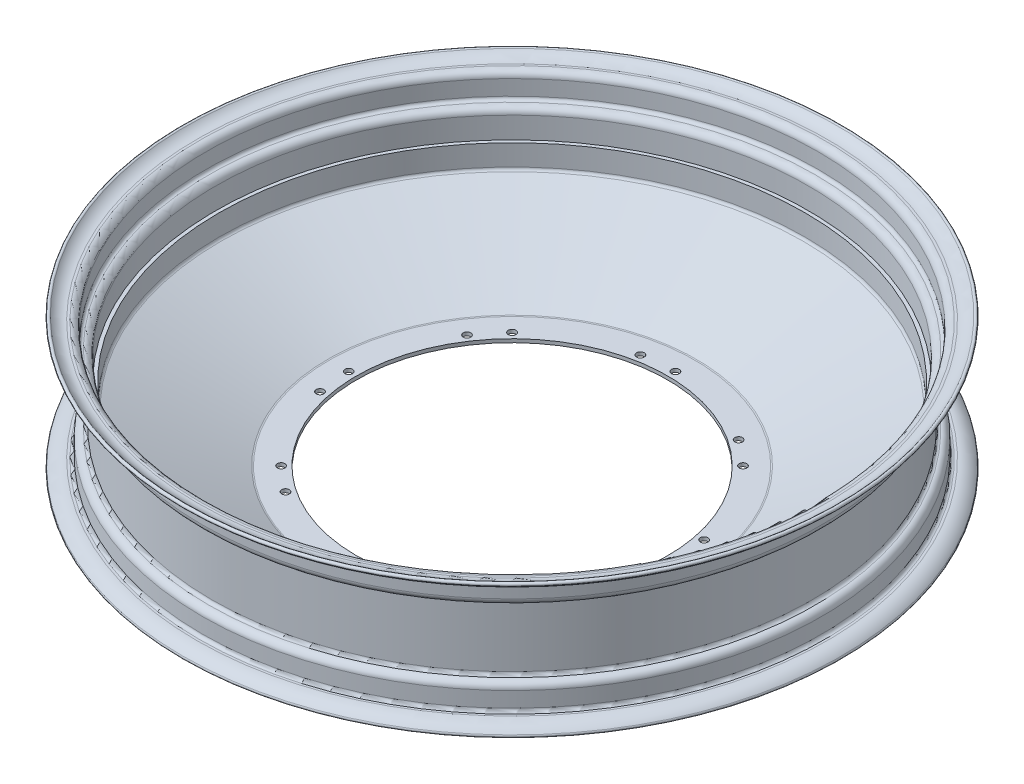
SolidWorks part; units mm, degrees
material "6061-T6 (SS)"
ref_plane "Front Plane" through (0, 0, 0) normal (0, 0, 1) x (1, 0, 0)
ref_plane "Top Plane" through (0, 0, 0) normal (0, 1, 0) x (1, 0, 0)
ref_plane "Right Plane" through (0, 0, 0) normal (1, 0, 0) x (0, 0, -1)
sketch "Sketch3" plane through (0, 0, 0) normal (0, 0, 1) x (1, 0, 0)
  line L0 (-167.2903, -3.117) -> (0, 0) construction
  line L2 (-206.3572, 37.168) -> (-204.8586, 37.168)
  line L3 (-200.5767, 32.8816) -> (-200.587, 22.8667)
  line L9 (-198.587, 19.7217) -> (-186.9755, 19.7217) construction
  line L13 (-102, -47.2925) -> (-119.8323, -47.2925)
  line L15 (-121.5965, -46.912) -> (-191.4766, -15.2967)
  line L17 (-194.301, 2.5281) -> (-192.015, 2.5281)
  line L18 (-200.4193, -21.368) -> (-183.6675, -4.616) construction
  line L24 (-202.8627, 32.884) -> (-202.873, 22.8691)
  line L26 (-206.3572, 34.882) -> (-204.8586, 34.882)
  line L35 (-102, -45.0056) -> (-102, -47.2925)
  line L36 (-200.4029, 15.0741) -> (-183.65, -1.6215) construction
  line L37 (-167.2903, -3.117) -> (-212.0495, -3.117) construction
  line L40 (-200.5767, 32.8816) -> (-200.589, 20.8706) construction
  line L41 (0, 240.889) -> (0, -99.5724) construction
  line L44 (-178.7195, -0.4999) -> (-178.7213, -5.7331) construction
  line L45 (-192.015, 2.5281) -> (-192.015, -11.2538)
  line L46 (-119.8323, -45.0065) -> (-102, -45.0056)
  line L47 (-181.0064, -3.0207) -> (-181.0064, -3.2073) construction
  line L48 (-198.8067, 16.7107) -> (-182.0364, -0.0021) construction
  line L49 (-198.8174, -22.999) -> (-182.0511, -6.2324) construction
  line L53 (-194.301, 16.5787) -> (-194.301, 2.5281)
  line L54 (-196.587, 16.5766) -> (-196.587, -22.8107)
  line L55 (-202.8627, 32.884) -> (-202.875, 20.8729) construction
  line L56 (-198.587, 20.8647) -> (-198.587, 18.5787) construction
  line L57 (-198.587, -27.0988) -> (-198.587, -24.8128) construction
  line L62 (-200.5711, -39.118) -> (-200.5712, -27.1182) construction
  line L63 (-206.3572, -43.404) -> (-204.8571, -43.404) construction
  line L64 (-202.8571, -39.118) -> (-202.8572, -27.1182) construction
  line L65 (-206.3572, -41.118) -> (-204.8571, -41.118) construction
  line L66 (-198.587, -25.9558) -> (-186.9755, -25.9558) construction
  line L67 (-206.3572, -41.1161) -> (-204.8586, -41.1161)
  line L68 (-202.8627, -39.1181) -> (-202.873, -29.1032)
  line L69 (-200.5767, -39.1157) -> (-200.587, -29.1008)
  line L70 (-206.3572, -43.4021) -> (-204.8586, -43.4021)
  line L72 (-120.6542, -44.8292) -> (-190.8394, -13.0759)
  line L73 (-120.6542, -44.8292) -> (-193.3587, -11.9362) construction
  line L74 (-104.286, -45.0065) -> (-119.8323, -45.0065) construction
  line L75 (-194.301, -17.1189) -> (-194.301, -22.8128)
  line L76 (-121.5965, -46.912) -> (-194.301, -14.0189) construction
  line L77 (-104.286, -45.0056) -> (-104.286, -45.0065) construction
  arc A0 (-213.9267, 40.5243) -> (-206.3572, 37.168) centre (-206.3572, 47.382) ccw
  arc A1 (-200.5767, 32.8816) -> (-204.8586, 37.168) centre (-204.8586, 32.886) ccw
  arc A11 (-182.0364, -0.0021) -> (-178.7195, -0.4999) centre (-180.0399, 2.0022) ccw construction
  arc A12 (-119.8323, -47.2925) -> (-121.5965, -46.912) centre (-119.8323, -43.0125) cw
  arc A13 (-178.7213, -5.7331) -> (-182.0511, -6.2324) centre (-180.0485, -8.2349) ccw construction
  arc A14 (-213.9267, 40.5243) -> (-215.6209, 38.9895) centre (-214.7738, 39.7569) ccw
  arc A17 (-183.65, -1.6215) -> (-181.0064, -3.0207) centre (-180.0399, 2.0022) ccw construction
  arc A24 (-202.8627, 32.884) -> (-204.8586, 34.882) centre (-204.8586, 32.886) ccw
  arc A28 (-215.6209, 38.9895) -> (-206.3572, 34.882) centre (-206.3572, 47.382) ccw
  arc A31 (-181.0064, -3.2073) -> (-183.6675, -4.616) centre (-180.0485, -8.2349) ccw construction
  arc A37 (-200.589, 20.8706) -> (-198.8067, 16.7107) centre (-194.8572, 20.8647) ccw construction
  arc A38 (-202.875, 20.8729) -> (-200.4029, 15.0741) centre (-194.8572, 20.8647) ccw construction
  arc A42 (-198.587, 20.8647) -> (-200.587, 22.8667) centre (-198.587, 22.8647) cw
  arc A44 (-202.873, 22.8691) -> (-198.587, 18.5787) centre (-198.587, 22.8647) ccw
  arc A49 (-119.8323, -45.0065) -> (-120.6542, -44.8292) centre (-119.8323, -43.0125) cw
  arc A54 (-198.587, -27.0988) -> (-194.301, -22.8128) centre (-198.587, -22.8128) ccw
  arc A55 (-198.587, -24.8128) -> (-196.587, -22.8107) centre (-198.587, -22.8128) ccw
  arc A56 (-198.587, 18.5787) -> (-196.587, 16.5766) centre (-198.587, 16.5787) cw
  arc A57 (-198.587, 20.8647) -> (-194.301, 16.5787) centre (-198.587, 16.5787) cw
  arc A58 (-198.8174, -22.999) -> (-200.5712, -27.1182) centre (-194.8572, -27.1181) ccw construction
  arc A59 (-204.8571, -43.404) -> (-200.5711, -39.118) centre (-204.8571, -39.118) ccw construction
  arc A60 (-206.3572, -43.404) -> (-213.9267, -46.7603) centre (-206.3572, -53.618) ccw construction
  arc A61 (-204.8571, -41.118) -> (-202.8571, -39.118) centre (-204.8571, -39.118) ccw construction
  arc A62 (-200.4193, -21.368) -> (-202.8572, -27.1182) centre (-194.8572, -27.1181) ccw construction
  arc A63 (-206.3572, -41.118) -> (-215.6209, -45.2255) centre (-206.3572, -53.618) ccw construction
  arc A64 (-198.587, -24.8128) -> (-202.873, -29.1032) centre (-198.587, -29.0988) ccw
  arc A65 (-198.587, -27.0988) -> (-200.587, -29.1008) centre (-198.587, -29.0988) ccw
  arc A66 (-215.6209, -45.2236) -> (-206.3572, -41.1161) centre (-206.3572, -53.6161) cw
  arc A67 (-202.8627, -39.1181) -> (-204.8586, -41.1161) centre (-204.8586, -39.1201) cw
  arc A68 (-213.9267, -46.7584) -> (-215.6209, -45.2236) centre (-214.7738, -45.991) cw
  arc A69 (-200.5767, -39.1157) -> (-204.8586, -43.4021) centre (-204.8586, -39.1201) cw
  arc A70 (-213.9267, -46.7584) -> (-206.3572, -43.4021) centre (-206.3572, -53.6161) cw
  arc A71 (-192.015, -11.2538) -> (-190.8394, -13.0759) centre (-190.015, -11.2538) ccw
  arc A72 (-191.4766, -15.2967) -> (-194.301, -17.1189) centre (-192.301, -17.1189) ccw
  point P103 (-194.301, -3.117)
  point P121 (-196.587, -3.117)
  point P130 (-194.301, -14.0189)
  dimension "D1" = 41.8885
  dimension "D3" = 4.282
  dimension "D8" = 4.28
  dimension "D5" = 1.996
  dimension "D6" = 2
  dimension "D9" = 2
  dimension "D10" = 2
  dimension "D2" = 2.286
  dimension "D4" = 2.286
revolve "Revolve2" add sketch "Sketch3" angle 360 about L41
sketch "Sketch4" plane through (0, 0, 0) normal (0, 1, 0) x (1, 0, 0)
  line L0 (0, 0) -> (0, 107) construction
  line L1 (0, 0) -> (-20.8747, 104.944) construction
  circle A0 centre (0, 107) radius 2.5
  circle A1 centre (-3884.1816, -9484.2438) radius 2.5
  circle A2 centre (-13412.7463, -13519.7463) radius 2.5
  circle A3 centre (-23003.9901, -9635.5647) radius 2.5
  circle A4 centre (-27039.4925, -107) radius 2.5
  circle A5 centre (-23155.3109, 9484.2438) radius 2.5
  circle A6 centre (-13626.7463, 13519.7463) radius 2.5
  circle A7 centre (-4035.5024, 9635.5647) radius 2.5
  circle A8 centre (-20.8747, 104.944) radius 2.5
  circle A9 centre (-3900.396, -9470.937) radius 2.5
  circle A10 centre (-13414.8022, -13498.8716) radius 2.5
  circle A11 centre (-22990.6833, -9619.3503) radius 2.5
  circle A12 centre (-27018.6178, -104.944) radius 2.5
  circle A13 centre (-23139.0965, 9470.937) radius 2.5
  circle A14 centre (-13624.6903, 13498.8716) radius 2.5
  circle A15 centre (-4048.8092, 9619.3503) radius 2.5
  circle A16 centre (75.6604, 75.6604) radius 2.5
  circle A17 centre (59.446, 88.9672) radius 2.5
  circle A18 centre (107, 0) radius 2.5
  circle A19 centre (104.944, 20.8747) radius 2.5
  circle A20 centre (75.6604, -75.6604) radius 2.5
  circle A21 centre (88.9672, -59.446) radius 2.5
  circle A22 centre (0, -107) radius 2.5
  circle A23 centre (20.8747, -104.944) radius 2.5
  circle A24 centre (-75.6604, -75.6604) radius 2.5
  circle A25 centre (-59.446, -88.9672) radius 2.5
  circle A26 centre (-107, 0) radius 2.5
  circle A27 centre (-104.944, -20.8747) radius 2.5
  circle A28 centre (-75.6604, 75.6604) radius 2.5
  circle A29 centre (-88.9672, 59.446) radius 2.5
  point P19 (-13519.7463, 0)
  point P37 (-13519.7463, 0)
  point P67 (0, 0)
  dimension "D1" = 107
  dimension "D2" = 5
  dimension "D4" = 11.25
  dimension "D5" = 8
  dimension "D3" = 8
  dimension "D6" = 8
extrude "Cut-Extrude3" cut sketch "Sketch4" against normal through all both and the other way through all
